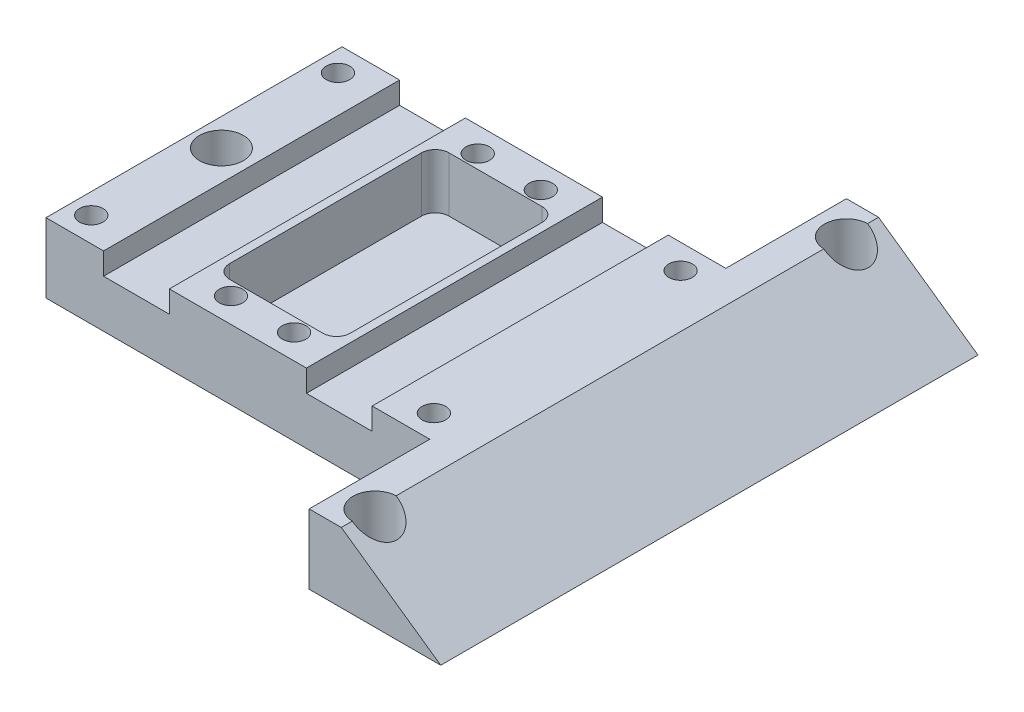
SolidWorks part; units mm, degrees
material "6063-T6"
ref_plane "Plano frontal" through (0, 0, 0) normal (0, 0, 1) x (1, 0, 0)
ref_plane "Plano superior" through (0, 0, 0) normal (0, 1, 0) x (1, 0, 0)
ref_plane "Plano direito" through (0, 0, 0) normal (1, 0, 0) x (0, 0, -1)
sketch "Esboço1" plane through (0, 0, 0) normal (0, 0, 1) x (1, 0, 0)
  line L1 (0, 0) -> (94, 0)
  line L5 (75.8625, 12.7) -> (0, 12.7)
  line L6 (0, 12.7) -> (0, 0)
  line L8 (75.8625, 12.7) -> (94, 0)
  dimension "D1" = 35
  dimension "D2" = 94
  dimension "D3" = 12.7
extrude "Ressalto-extrusão1" add sketch "Esboço1" along normal blind 98
sketch "Esboço4" plane through (0, 12.7, 0) normal (0, 1, 0) x (1, 0, 0)
  line L0 (75.8625, -98) -> (0, -98) construction
  line L5 (75.8625, 0) -> (0, 0) construction
  line L7 (33, -76) -> (33, -98)
  line L8 (33, -98) -> (0, -98)
  line L9 (0, -76) -> (0, -98)
  line L15 (33, 0) -> (0, 0)
  line L16 (33, 0) -> (33, -22)
  line L18 (0, 0) -> (0, -22)
  line L28 (0, -98) -> (0, 0) construction
  line L29 (70, -98) -> (37, -98)
  line L30 (70, -98) -> (70, -76)
  line L32 (37, -98) -> (37, -76)
  line L33 (70, 0) -> (37, 0)
  line L34 (70, 0) -> (70, -22)
  line L36 (37, 0) -> (37, -22)
  line L56 (70, -22) -> (37, -22)
  line L57 (33, -22) -> (0, -22)
  line L58 (0, -76) -> (33, -76)
  line L59 (37, -76) -> (70, -76)
  dimension "D1" = 22
  dimension "D3" = 33
  dimension "D4" = 22
  dimension "D5" = 33
  dimension "D6" = 22
  dimension "D7" = 22
  dimension "D8" = 4
  dimension "D9" = 33
  dimension "D10" = 4
  dimension "D11" = 33
  dimension "D12" = 22
  dimension "D19" = 22
  dimension "D21" = 22
  dimension "D23" = 22
extrude "Corte-extrusão3" cut sketch "Esboço4" against normal blind 25
sketch "Esboço2" plane through (0, 12.7, 0) normal (0, 1, 0) x (1, 0, 0)
  line L0 (76, -6) -> (76, -92) construction
  line L4 (76, -49) -> (0, -49) construction
  line L5 (75.8625, 0) -> (70, 0) construction
  line L6 (75.8625, -98) -> (70, -98) construction
  line L7 (0, -76) -> (0, -22) construction
  line L8 (0, -76) -> (0, -22) construction
  line L9 (70, -98) -> (70, -76) construction
  circle A0 centre (76, -92) radius 4
  circle A1 centre (76, -6) radius 4
  circle A2 centre (5, -49) radius 4
  dimension "D3" = 8
  dimension "D4" = 8
  dimension "D6" = 8
  dimension "D1" = 6
  dimension "D5" = 6
  dimension "D7" = 5
  dimension "D8" = 6
extrude "Corte-extrusão1" cut sketch "Esboço2" against normal blind 98
sketch "Esboço10" plane through (0, 0, 76) normal (0, 0, 1) x (1, 0, 0)
  line L0 (16.5, 12.7) -> (16.5, 0) construction
  line L1 (33, 12.7) -> (0, 12.7) construction
  line L2 (33, 0) -> (0, 0) construction
  line L3 (53.5, 12.7) -> (53.5, 0) construction
  line L4 (37, 12.7) -> (33, 12.7) construction
  line L5 (35, 12.7) -> (35, 0) construction
  line L6 (33, 0) -> (37, 0) construction
  line L7 (10.5, 12.7) -> (22.5, 12.7)
  line L8 (10.5, 12.7) -> (10.5, 8.7)
  line L9 (10.5, 8.7) -> (22.5, 8.7)
  line L10 (22.5, 12.7) -> (22.5, 8.7)
  line L11 (47.5, 12.7) -> (47.5, 8.7)
  line L12 (59.5, 8.7) -> (47.5, 8.7)
  line L13 (59.5, 12.7) -> (59.5, 8.7)
  line L14 (59.5, 12.7) -> (47.5, 12.7)
  dimension "D1" = 4
  dimension "D2" = 6
  dimension "D3" = 6
extrude "Corte-extrusão8" cut sketch "Esboço10" against normal through all
sketch "Esboço11" plane through (0, 12.7, 0) normal (0, 1, 0) x (1, 0, 0)
  line L0 (0, -26.5) -> (29.25, -26.5) construction
  line L1 (0, -76) -> (0, -22) construction
  line L2 (29.25, -26.5) -> (29.25, -71.5) construction
  line L3 (29.25, -71.5) -> (0, -71.5) construction
  line L4 (0, -22) -> (10.5, -22) construction
  line L5 (10.5, -76) -> (0, -76) construction
  line L6 (40.75, -26.5) -> (66.25, -26.5) construction
  line L7 (66.25, -26.5) -> (66.25, -71.5) construction
  line L8 (66.25, -71.5) -> (40.75, -71.5) construction
  line L9 (47.5, -22) -> (47.5, -76) construction
  circle A0 centre (29.25, -26.5) radius 1.6
  circle A1 centre (29.25, -71.5) radius 1.6
  circle A2 centre (3.75, -71.5) radius 1.6
  circle A3 centre (3.75, -26.5) radius 1.6
  circle A4 centre (40.75, -26.5) radius 1.6
  circle A5 centre (66.25, -26.5) radius 1.6
  circle A6 centre (66.25, -71.5) radius 1.6
  circle A7 centre (40.75, -71.5) radius 1.6
  dimension "D6" = 3.2
  dimension "D7" = 3.2
  dimension "D8" = 3.2
  dimension "D9" = 3.2
  dimension "D13" = 3.2
  dimension "D14" = 3.2
  dimension "D15" = 3.2
  dimension "D16" = 3.2
  dimension "D1" = 4.5
  dimension "D2" = 4.5
  dimension "D3" = 3.75
  dimension "D4" = 3.75
  dimension "D5" = 25.5
  dimension "D10" = 6.75
  dimension "D11" = 25.5
  dimension "D12" = 6.75
  dimension "D17" = 45
extrude "Corte-extrusão9" cut sketch "Esboço11" against normal blind 20
sketch "Esboço12" plane through (0, 12.7, 0) normal (0, 1, 0) x (1, 0, 0)
  line L1 (46, -29) -> (24, -29)
  line L2 (46, -29) -> (46, -69)
  line L3 (46, -69) -> (24, -69)
  line L4 (24, -29) -> (24, -69)
  line L5 (33, -76) -> (22.5, -76) construction
  line L7 (47.5, -22) -> (47.5, -76) construction
  dimension "D1" = 1.5
  dimension "2" = 22
  dimension "D2" = 40
  dimension "D3" = 7
extrude "Corte-extrusão10" cut sketch "Esboço12" against normal blind 10
fillet "Filete1" radius 2.5 4 edges at (24, 7.7, 69) (24, 7.7, 29) (46, 7.7, 29) (46, 7.7, 69)
hole_wizard "Escareado para parafuso Allen sextavado escareado de M41" positions "Esboço13" profile "Esboço14" countersink size "M4" standard "ISO" end condition through all
sketch "Esboço13" plane through (0, 0, 0) normal (0, -1, 0) x (-1, 0, 0)
  circle A0 centre (-3.75, -71.5) radius 1.6 construction
  point P0 (-66.25, -71.5)
  point P3 (-66.25, -26.5)
  point P6 (-40.75, -26.5)
  point P9 (-29.25, -26.5)
  point P12 (-29.25, -71.5)
  point P15 (-40.75, -71.5)
  point P18 (-3.75, -71.5)
  point P21 (-3.75, -26.5)
  dimension "D1" = 45
  dimension "D2" = 25.5
  dimension "D3" = 25.5
  dimension "D4" = 11.5
  dimension "D5" = 62.5
sketch "Esboço14" plane through (66.25, 0, 71.5) normal (1, 0, 0) x (0, 0, -1)
  line L0 (0, 0) -> (0, 12.7)
  line L1 (0, 12.7) -> (2.15, 12.7)
  line L2 (2.15, 12.7) -> (2.15, 2.33)
  line L3 (2.15, 2.33) -> (4.48, 0)
  line L5 (4.48, 0) -> (0, 0)
  line L6 (-2.15, 2.33) -> (-4.48, 0) construction
  line L11 (0, -6.35) -> (0, 107.95) construction
  dimension "Thru Hole Dia." = 4.3
  dimension "Thru Hole Depth" = 12.7
  dimension "Near C'Sink Dia." = 8.96
  dimension "Near C'Sink Angle" = 90
sketch "Esboço15" plane through (0, 12.7, 0) normal (0, 1, 0) x (1, 0, 0)
  line L0 (33, -98) -> (33, -76) construction
  line L1 (37, 0) -> (33, 0)
  line L2 (37, 0) -> (37, -22)
  line L3 (37, -22) -> (33, -22)
  line L4 (33, 0) -> (33, -22)
  line L5 (37, -98) -> (33, -98)
  line L6 (37, -98) -> (37, -76)
  line L7 (37, -76) -> (33, -76)
  line L8 (33, -98) -> (33, -76)
extrude "Corte-extrusão11" cut sketch "Esboço15" against normal through all
